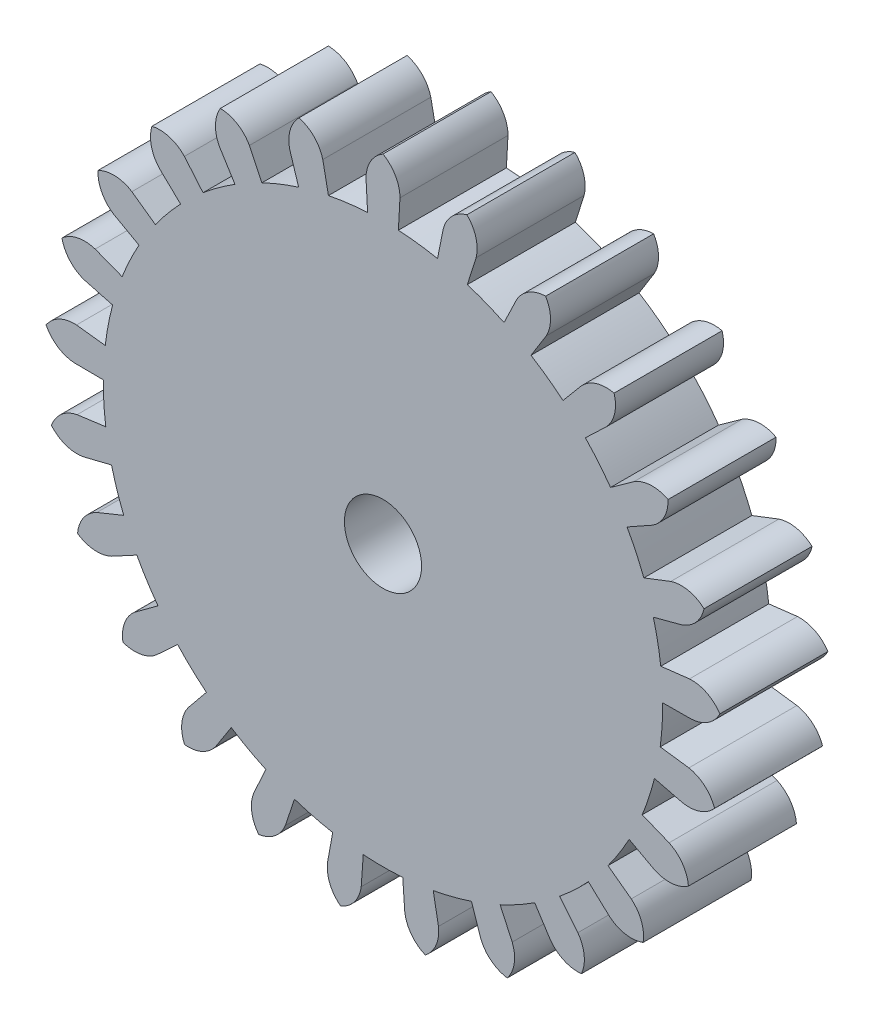
SolidWorks part; units mm, degrees
ref_plane "Front Plane" through (0, 0, 0) normal (0, 0, 1) x (1, 0, 0)
ref_plane "Top Plane" through (0, 0, 0) normal (0, 1, 0) x (1, 0, 0)
ref_plane "Right Plane" through (0, 0, 0) normal (1, 0, 0) x (0, 0, -1)
sketch "Sketch1" plane through (0, 0, 0) normal (0, 0, 1) x (1, 0, 0)
  line L0 (-0.55, 0) -> (0.55, 0) construction
  line L1 (-0.55, 0) -> (0.55, 0) construction
  line L2 (-0.55, -30.0151) -> (-0.4984, -30.9512)
  line L3 (0.4984, -30.9512) -> (0.55, -30.0151)
  line L4 (0, -29.0625) -> (0, -30) construction
  circle A0 centre (0, -40) radius 10 construction
  circle A1 centre (0, -40) radius 10 construction
  arc A2 (0, -29.0625) -> (-0.55, -30.0151) centre (0.55, -30.0151) ccw
  arc A3 (0.55, -30.0151) -> (0, -29.0625) centre (-0.55, -30.0151) ccw
  circle A4 centre (0, -40) radius 9.0625
extrude "Boss-Extrude1" add sketch "Sketch1" along normal blind 3.5 contours A4 L3 A3 A2 L2 | A4
pattern_circular "CirPattern1" count 25 over 360 about axis through (0, -40, 0) along (0, 0, 1) of "Boss-Extrude1"
sketch "Sketch3" plane through (0, 0, 0) normal (0, 0, -1) x (-1, 0, 0)
  circle A0 centre (0, -40) radius 4 construction
  circle A1 centre (0, -40) radius 4
extrude "Boss-Extrude2" add sketch "Sketch3" along normal up to vertex (2 mm away)
sketch "Sketch2" plane through (0, 0, 3.5) normal (0, 0, 1) x (1, 0, 0)
  circle A0 centre (0, -40) radius 1.25 construction
  circle A1 centre (0, -40) radius 1.25
extrude "Cut-Extrude1" cut sketch "Sketch2" against normal through all
equation "\"teeth\"= 25"
equation "\"D1@CirPattern1\"=\"teeth\""
